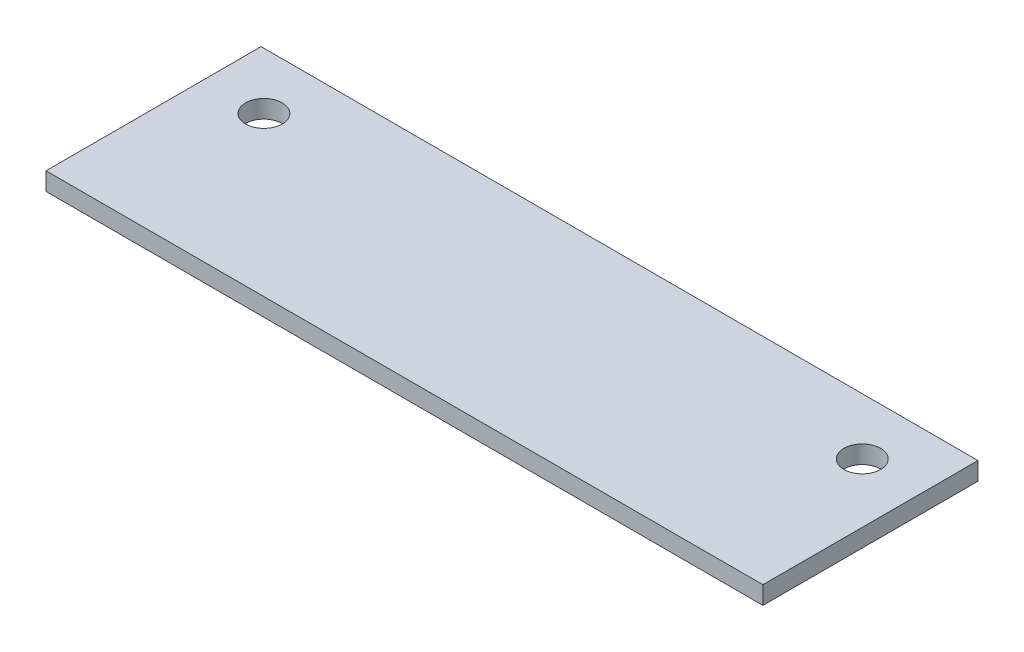
SolidWorks part; units mm, degrees
material "AISI 4130 Steel, annealed at 865C"
ref_plane "X-Y Datum" through (0, 0, 0) normal (0, 0, 1) x (1, 0, 0)
ref_plane "X-Z Datum" through (0, 0, 0) normal (0, 1, 0) x (1, 0, 0)
ref_plane "Y-Z Datum" through (0, 0, 0) normal (1, 0, 0) x (0, 0, -1)
sketch "Sketch1" plane through (0, 0, 0) normal (0, 1, 0) x (1, 0, 0)
  line L1 (-63.5, -38.1) -> (63.5, -38.1)
  line L2 (-63.5, -38.1) -> (-63.5, 38.1)
  line L3 (-63.5, 38.1) -> (63.5, 38.1)
  line L4 (63.5, -38.1) -> (63.5, 38.1)
  line L5 (-63.5, -38.1) -> (63.5, 38.1) construction
  line L6 (-63.5, 38.1) -> (63.5, -38.1) construction
  point P0 (0, 0)
  dimension "D1" = 127
  dimension "D2" = 76.2
extrude "Boss-Extrude1" add sketch "Sketch1" along normal blind 3.175 contours L3 L4 L1 L2
sketch "Sketch3" plane through (0, 3.175, 0) normal (0, 1, 0) x (1, 0, 0)
  line L0 (63.5, 0) -> (-63.5, 0)
  line L4 (-63.5, 38.1) -> (-63.5, -38.1)
  line L5 (-63.5, -38.1) -> (63.5, -38.1)
  line L6 (63.5, -38.1) -> (63.5, 38.1)
  line L7 (63.5, 38.1) -> (-63.5, 38.1)
  line L8 (-63.5, 38.1) -> (-63.5, -38.1)
  line L9 (-63.5, -38.1) -> (63.5, -38.1)
  line L10 (63.5, -38.1) -> (63.5, 38.1)
  line L11 (63.5, 38.1) -> (-63.5, 38.1)
  circle A0 centre (53, 28.1) radius 3.25 construction
  circle A1 centre (-53, 28.1) radius 3.25 construction
  circle A2 centre (53, 28.1) radius 3.25
  circle A3 centre (-53, 28.1) radius 3.25
  line M5 (-63.5, 38.1) -> (-63.5, -38.1)
  line M6 (-63.5, -38.1) -> (63.5, -38.1)
  line M7 (63.5, -38.1) -> (63.5, 38.1)
  dimension "D1" = 0
extrude "Cut-Extrude1" cut sketch "Sketch3" against normal through all contours L0 M7 M5 M6 | A3 | A2
